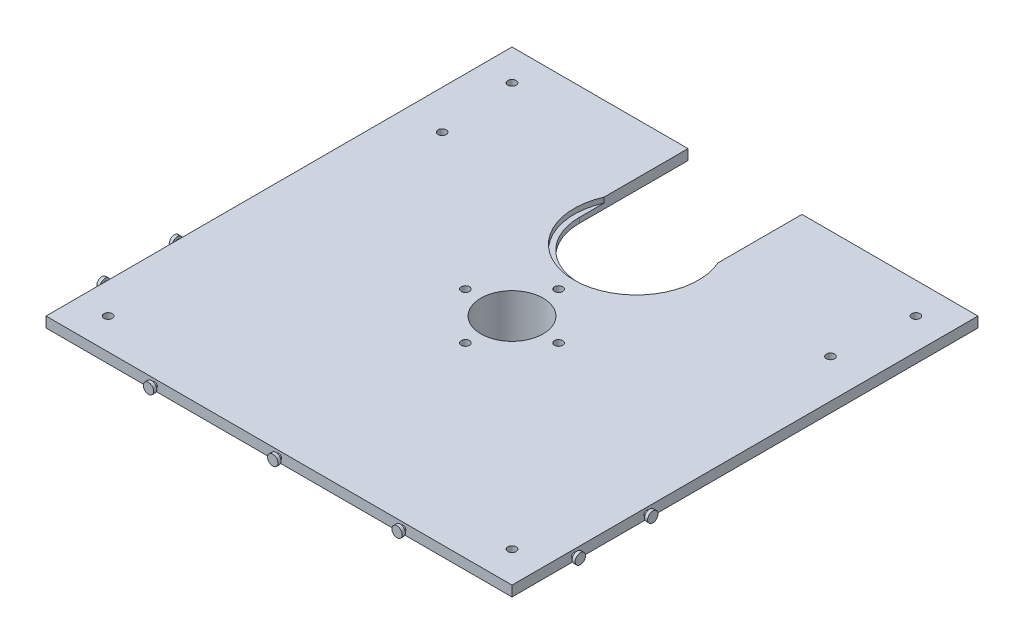
SolidWorks part; units mm, degrees
ref_plane "Alzado" through (0, 0, 0) normal (0, 0, 1) x (1, 0, 0)
ref_plane "Planta" through (0, 0, 0) normal (0, 1, 0) x (1, 0, 0)
ref_plane "Vista lateral" through (0, 0, 0) normal (1, 0, 0) x (0, 0, -1)
sketch "Croquis1" plane through (0, 0, 0) normal (0, 1, 0) x (1, 0, 0)
  line L1 (-225, -225) -> (225, -225)
  line L2 (-225, -225) -> (-225, 225)
  line L3 (-225, 225) -> (225, 225)
  line L4 (225, -225) -> (225, 225)
  line L5 (-225, -225) -> (225, 225) construction
  line L6 (-225, 225) -> (225, -225) construction
  circle A1 centre (0, 0) radius 30
  circle A2 centre (0, 0) radius 120 construction
  circle A3 centre (0, 120) radius 55
  point P16 (0, 0)
  dimension "D2" = 60
  dimension "D3" = 240
  dimension "D4" = 110
  dimension "D5" = 450
extrude "Saliente-Extruir1" add sketch "Croquis1" along normal blind 10
sketch "Croquis7" plane through (0, 10, 0) normal (0, 1, 0) x (1, 0, 0)
  line L1 (-225, 225) -> (-225, -225) construction
  line L2 (225, -225) -> (225, 225) construction
  circle A0 centre (-195, 195) radius 4
  circle A1 centre (195, 195) radius 4
  circle A2 centre (195, -195) radius 4
  circle A3 centre (-195, -195) radius 4
  circle A4 centre (-45, 0) radius 4
  circle A5 centre (0, 45) radius 4
  circle A6 centre (0, -45) radius 4
  circle A7 centre (45, 0) radius 4
  circle A8 centre (-187.5, 120) radius 4
  circle A9 centre (187.5, 120) radius 4
  dimension "D1" = 8
  dimension "D2" = 8
  dimension "D3" = 8
  dimension "D4" = 8
  dimension "D5" = 8
  dimension "D6" = 8
  dimension "D7" = 8
  dimension "D8" = 8
  dimension "D19" = 8
  dimension "D20" = 8
  dimension "D9" = 195
  dimension "D10" = 390
  dimension "D11" = 195
  dimension "D12" = 390
  dimension "D13" = 45
  dimension "D14" = 90
  dimension "D15" = 45
  dimension "D16" = 90
  dimension "D17" = 105
  dimension "D18" = 37.5
  dimension "D21" = 37.5
extrude "Cortar-Extruir6" cut sketch "Croquis7" against normal through all
sketch "Croquis8" plane through (0, 10, 0) normal (0, 1, 0) x (1, 0, 0)
  line L4 (225, -225) -> (225, 225)
  line L5 (225, 225) -> (-225, 225)
  line L6 (-225, 225) -> (-225, -225)
  line L7 (-225, -225) -> (225, -225)
  line L8 (225, -225) -> (225, 225)
  line L9 (225, 225) -> (-225, 225)
  line L10 (-225, 225) -> (-225, -225)
  line L11 (-225, -225) -> (225, -225)
  circle A0 centre (0, 120) radius 55 construction
  circle A1 centre (0, 120) radius 55
  circle A2 centre (0, 120) radius 60
  circle M19 centre (0, 120) radius 55
  dimension "D2" = 120
  dimension "D1" = 0
extrude "Cortar-Extruir7" cut sketch "Croquis8" against normal blind 5 contours A2 M19
sketch "Croquis9" plane through (0, 10, 0) normal (0, 1, 0) x (1, 0, 0)
  line L0 (0, 120) -> (55, 120)
  line L1 (55, 120) -> (55, 225)
  line L2 (225, 225) -> (-225, 225) construction
  line L3 (55, 225) -> (-55, 225)
  line L4 (-55, 225) -> (-55, 120)
  line L5 (-55, 120) -> (0, 120)
  circle A0 centre (0, 120) radius 55 construction
  circle A1 centre (0, 120) radius 55
  circle M1 centre (0, 120) radius 60
  line M11 (225, 225) -> (-225, 225)
extrude "Cortar-Extruir8" cut sketch "Croquis9" against normal through all contours L4 L1 M11 M1 | A1 L1 L4 M1
sketch "Croquis10" plane through (0, 0, 0) normal (0, -1, 0) x (1, 0, 0)
  circle A0 centre (0, 0) radius 30 construction
  circle A1 centre (0, 0) radius 30
  circle A2 centre (0, 0) radius 35
  dimension "D1" = 70
extrude "Saliente-Extruir2" add sketch "Croquis10" along normal blind 100
sketch "Croquis11" plane through (225, 0, 0) normal (1, 0, 0) x (0, 0, -1)
  line L0 (-225, 5) -> (225, 5) construction
  line L1 (-225, 10) -> (225, 10) construction
  line L2 (-225, 10) -> (-225, 0) construction
  line L3 (-225, 0) -> (225, 0) construction
  line L4 (225, 10) -> (225, 0) construction
  circle A0 centre (-165, 5) radius 2.5
  circle A1 centre (-95, 5) radius 2.5
  dimension "D1" = 5
  dimension "D2" = 5
  dimension "D3" = 70
  dimension "D4" = 60
extrude "Saliente-Extruir3" add sketch "Croquis11" along normal blind 3
sketch "Croquis12" plane through (228, 0, 0) normal (1, 0, 0) x (0, 0, -1)
  circle A1 centre (-165, 5) radius 2.5
  circle A2 centre (-165, 5) radius 2.5 construction
  circle A3 centre (-165, 5) radius 5
  circle A4 centre (-95, 5) radius 5
  dimension "D2" = 10
  dimension "D3" = 10
  dimension "D1" = 0
extrude "Saliente-Extruir4" add sketch "Croquis12" along normal blind 3
mirror "Simetría1" about plane through (0, 0, 0) normal (1, 0, 0) of "Saliente-Extruir3", "Saliente-Extruir4"
sketch "Croquis14" plane through (0, 0, 225) normal (0, 0, 1) x (1, 0, 0)
  line L0 (-225, 5) -> (225, 5) construction
  line L1 (-225, 10) -> (225, 10) construction
  line L2 (-225, 10) -> (-225, 0) construction
  line L3 (-225, 0) -> (225, 0) construction
  line L4 (225, 10) -> (225, 0) construction
  circle A0 centre (-120, 5) radius 2.5
  circle A1 centre (0, 5) radius 2.5
  circle A2 centre (120, 5) radius 2.5
  dimension "D1" = 5
  dimension "D2" = 5
  dimension "D3" = 5
  dimension "D4" = 120
  dimension "D5" = 120
extrude "Saliente-Extruir5" add sketch "Croquis14" along normal blind 3
sketch "Croquis15" plane through (0, 0, 228) normal (0, 0, 1) x (1, 0, 0)
  circle A0 centre (120, 5) radius 2.5 construction
  circle A1 centre (0, 5) radius 2.5 construction
  circle A2 centre (-120, 5) radius 2.5 construction
  circle A3 centre (120, 5) radius 2.5 construction
  circle A4 centre (0, 5) radius 2.5 construction
  circle A5 centre (-120, 5) radius 2.5 construction
  circle A6 centre (-120, 5) radius 5
  circle A7 centre (0, 5) radius 5
  circle A8 centre (120, 5) radius 5
  dimension "D1" = 10
  dimension "D2" = 10
  dimension "D3" = 10
extrude "Saliente-Extruir6" add sketch "Croquis15" along normal blind 3
